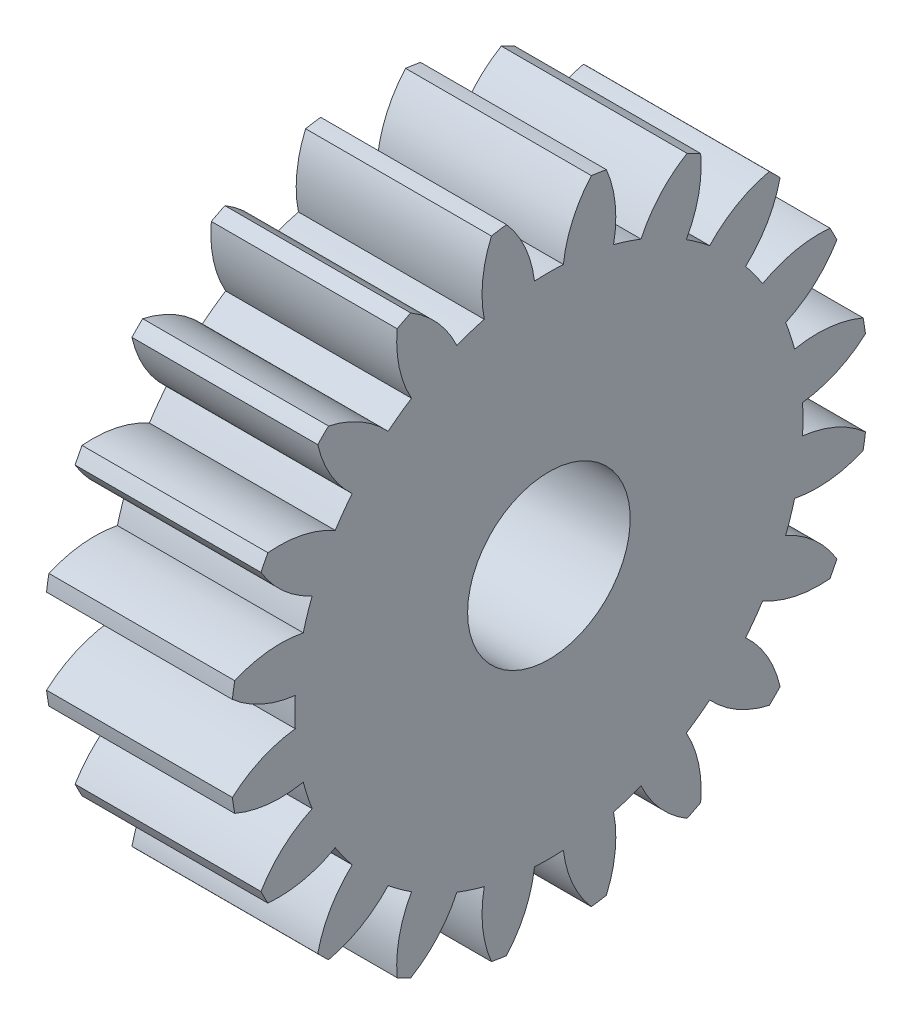
SolidWorks part; units mm, degrees
ref_plane "Plane1" through (0, 0, 0) normal (0, 0, 1) x (1, 0, 0)
ref_plane "Plane2" through (0, 0, 0) normal (0, 1, 0) x (1, 0, 0)
ref_plane "Plane3" through (0, 0, 0) normal (1, 0, 0) x (0, 0, -1)
sketch "HoldingSke" plane through (0, 0, 0) normal (0, 1, 0) x (1, 0, 0)
  line L0 (0, 0) -> (0.7518, -0.2736)
  line L1 (-15, 0) -> (100, 0) construction
  line L2 (0, 0) -> (-2.1039, 2.3779)
  line L3 (0, 0) -> (-11.863, 4.5341)
  line L4 (0, 0) -> (8.1152, 2.9537)
  line L5 (0, 0) -> (-46.8476, -17.4728)
  line L6 (0, 0) -> (-6.6317, -4.4744)
  line L7 (-2.1039, 2.3779) -> (8.6586, 51.2059)
  line L8 (-76.2, 54.61) -> (-75.2, 54.61)
  line L9 (-71.009, 38.7566) -> (-53.1078, 45.2721)
  line L10 (-76.2, 71.12) -> (104.1128, 71.12)
  line L11 (0, 0) -> (-8, 0)
  line L12 (-76.2, 101.6) -> (-76.155, 101.6)
  line L13 (24.9733, 27.94) -> (52.9518, 28.4284)
  line L14 (24.9733, 27.94) -> (24.9743, 27.94)
  line L15 (24.9733, 27.94) -> (100.4006, 29.5858)
  line L16 (-63.627, -1.25) -> (-12.827, -1.25)
  circle A0 centre (0, 0) radius 3.5
  circle A1 centre (0, 0) radius 10.9365
  circle A2 centre (0, 0) radius 37.5
  circle A3 centre (0, 0) radius 3.5
  dimension "MHD" = 21.873
  dimension "Hub_dia" = 75
  dimension "Bore" = 7
  dimension "MBD" = 7
  dimension "Num_teeth" = 20
  dimension "Pitch" = 0.8
  dimension "Overall_len" = 50
  dimension "Show_teeth" = 20
  dimension "Thickness" = 8
  dimension "OAL" = 50.0001
  dimension "T_dim" = 1
  dimension "Ap" = 20
  dimension "H" = 19.05
  dimension "Pitch_radius" = 180.3128
  dimension "Width" = 8
  dimension "Backlash" = 0.045
  dimension "Addendum_fac" = 1
  dimension "Dedendum_fac" = 1.25
  dimension "Clearance_fac" = 0.25
  dimension "Dedendum_add" = 0.001
  dimension "Module" = 1.25
sketch "BasProSke" plane through (0, 0, 0) normal (0, 1, 0) x (1, 0, 0)
  line L0 (-10, 0) -> (60, 0) construction
  line L1 (0, 0) -> (0, 13.75)
  line L2 (0, 0) -> (8, 0)
  line L3 (8, 0) -> (8, 13.75)
  line L4 (8, 13.75) -> (0, 13.75)
  dimension "Thickness" = 8
  dimension "Diameter" = 27.5
revolve "Base-Revolve" add sketch "BasProSke" angle 360 about L0
sketch "TooCutSke" plane through (0, 0, 0) normal (1, 0, 0) x (0, 0, -1)
  line L1 (0, 0) -> (0, 107) construction
  line L2 (0, 0) -> (-1.0594, 12.455) construction
  line L3 (0, 0) -> (-3.9007, 24.6278) construction
  line L4 (-1.0594, 12.455) -> (-1.9503, 12.3139) construction
  arc A0 (0.6211, 10.9188) -> (-0.6211, 10.9188) centre (0, 0) ccw
  arc A1 (1.8466, 13.6511) -> (-1.8466, 13.6511) centre (0, 0) ccw
  circle A2 centre (0, 0) radius 12.5 construction
  circle A3 centre (0, 0) radius 11.7462 construction
  arc A4 (-0.6211, 10.9188) -> (-1.8466, 13.6511) centre (-5.5866, 10.3326) ccw
  arc A5 (1.8466, 13.6511) -> (0.6211, 10.9188) centre (5.5866, 10.3326) ccw
  dimension "Root_dia" = 21.873
  dimension "Overcut_dia" = 27.5508
  dimension "Pitch_dia" = 25
  dimension "Base_dia" = 23.4923
  dimension "Flank_rad" = 5
  dimension "Half_ang" = 9
  dimension "Half_CT" = 0.902
extrude "ToothCut" cut sketch "TooCutSke" along normal through all
fillet "Breaks" [suppressed] radius 0.025
fillet "RootFillets" [suppressed] radius 0.3135
pattern_circular "TeethCuts" count 20 every 18 about axis through (-10, 0, 0) along (1, 0, 0) of "ToothCut", "RootFillets", "Breaks"
sketch "HubNeaOneSke" plane through (0, 0, 0) normal (-1, 0, 0) x (0, 0, 1)
  circle A0 centre (0, 0) radius 10.9365
  dimension "Diameter" = 21.873
extrude "HubNearOne" [suppressed] add sketch "HubNeaOneSke" along normal blind 42.0001
sketch "HubNeaBotSke" plane through (0, 0, 0) normal (-1, 0, 0) x (0, 0, 1)
  circle A0 centre (0, 0) radius 10.9365
  dimension "Diameter" = 21.873
extrude "HubNearBoth" [suppressed] add sketch "HubNeaBotSke" along normal blind 21
ref_plane "FarPln" through (8, 0, 0) normal (1, 0, 0) x (0, 0, -1)
sketch "HubFarSke" plane through (8, 0, 0) normal (1, 0, 0) x (0, 0, -1)
  circle A0 centre (0, 0) radius 10.9365
  dimension "Diameter" = 21.873
extrude "HubFar" [suppressed] add sketch "HubFarSke" along normal blind 21
sketch "BorSke" plane through (0, 0, 0) normal (1, 0, 0) x (0, 0, -1)
  circle A0 centre (0, 0) radius 3.5
  dimension "Diameter" = 7
extrude "Bore" cut sketch "BorSke" along normal mid plane 100.0001
sketch "KeySke" plane through (0, 0, 0) normal (1, 0, 0) x (0, 0, -1)
  line L0 (-1, 0) -> (-1, 4.5)
  line L1 (-1, 4.5) -> (1, 4.5)
  line L2 (1, 4.5) -> (1, 0)
  line L3 (0, 0) -> (0, 34) construction
  line L4 (-1, 0) -> (1, 0)
  dimension "Offset" = 4.5
  dimension "Width" = 2
extrude "Keyway" [suppressed] cut sketch "KeySke" along normal mid plane 100.0001
pattern_circular "Keyway2" [suppressed] count 2 every 90 about axis through (-10, 0, 0) along (1, 0, 0)
equation "' \"Module@HoldingSke\" = 6.35"
equation "' \"Num_teeth@HoldingSke\" = 12"
equation "' \"Ap@HoldingSke\" =  20"
equation "' \"Ap@HoldingSke\" = 20"
equation "' \"Width@HoldingSke\" = 0.5 * 25.4"
equation "' \"Hub_dia@HoldingSke\"= 1 * 25.4"
equation "' \"Hub_dia@HoldingSke\" = 1 * 25.4"
equation "' \"Overall_len@HoldingSke\" = 1.0 * 25.4"
equation "' \"Bore@HoldingSke\" = 0.75 * 25.4"
equation "' \"T_dim@HoldingSke\" = 0.1 * 25.4"
equation "' \"Width@KeySke\" = 0.25 * 25.4"
equation "' \"Show_teeth@HoldingSke\" = 13"
equation "' \"Backlash@HoldingSke\" = 0.009 * 25.4"
equation "' \"Addendum_fac@HoldingSke\" = 1.0"
equation "' \"Dedendum_fac@HoldingSke\" = 1.25"
equation "' \"Dedendum_add@HoldingSke\" = 0.00005 * 25.4"
equation "' \"Clearance_fac@HoldingSke\" = 0.25"
equation "\"Pitch@HoldingSke\" = 1 / \"Module@HoldingSke\""
equation "\"Overcut_dia@TooCutSke\" = (\"Num_teeth@HoldingSke\" + 2 * \"Addendum_fac@HoldingSke\") / \"Pitch@HoldingSke\" + 0.002 * 25.4"
equation "\"Pitch_dia@TooCutSke\" = \"Num_teeth@HoldingSke\" / \"Pitch@HoldingSke\""
equation "\"Base_dia@TooCutSke\" = \"Num_teeth@HoldingSke\" / \"Pitch@HoldingSke\" * cos((\"Ap@HoldingSke\"  * 3.14159265 / 180))"
equation "\"Root_dia@TooCutSke\" = (\"Num_teeth@HoldingSke\" + 2) / \"Pitch@HoldingSke\" - 2 * (\"Addendum_fac@HoldingSke\" + \"Dedendum_fac@HoldingSke\") / \"Pitch@HoldingSke\" - \"Dedendum_add@HoldingSke\" * 2"
equation "\"Half_ang@TooCutSke\" = 180 / \"Num_teeth@HoldingSke\""
equation "\"Half_CT@TooCutSke\" = \"Num_teeth@HoldingSke\" / \"Pitch@HoldingSke\" * sin((3.14159265 / 2 / \"Num_teeth@HoldingSke\")) / 2 - 7 * \"Backlash@HoldingSke\" / 4"
equation "\"Flank_rad@TooCutSke\" = \"Num_teeth@HoldingSke\" / \"Pitch@HoldingSke\" / 5"
equation "\"Radius@RootFillets\" = \"Clearance_fac@HoldingSke\" / \"Pitch@HoldingSke\" + \"Dedendum_add@HoldingSke\""
equation "\"Break_rad@Breaks\" = 0.02 / \"Pitch@HoldingSke\""
equation "\"Thickness@HoldingSke\" = \"Width@HoldingSke\""
equation "\"OAL@HoldingSke\" = \"Thickness@HoldingSke\""
equation "\"MHD@HoldingSke\" = (\"Num_teeth@HoldingSke\" + 2) / \"Pitch@HoldingSke\" - 2 * (\"Addendum_fac@HoldingSke\" + \"Dedendum_fac@HoldingSke\")  / \"Pitch@HoldingSke\" - \"Dedendum_add@HoldingSke\" * 2"
equation "\"MBD@HoldingSke\" = (\"Num_teeth@HoldingSke\" + 2) / \"Pitch@HoldingSke\" - 2 * (\"Addendum_fac@HoldingSke\" + \"Dedendum_fac@HoldingSke\")  / \"Pitch@HoldingSke\" - \"Dedendum_add@HoldingSke\" * 2 - 0.002 * 25.4"
equation "\"MHD@HoldingSke\" = ((sgn( \"MHD@HoldingSke\" - \"Hub_dia@HoldingSke\" )-1)*( \"MHD@HoldingSke\" - \"Hub_dia@HoldingSke\" ))/-2+ \"Hub_dia@HoldingSke\""
equation "\"MBD@HoldingSke\" = ((sgn( \"MBD@HoldingSke\" - \"Bore@HoldingSke\" )-1)*( \"MBD@HoldingSke\" - \"Bore@HoldingSke\" ))/-2+ \"Bore@HoldingSke\""
equation "\"OAL@HoldingSke\" = ((sgn( \"OAL@HoldingSke\" - \"Overall_len@HoldingSke\" )+1)*( \"OAL@HoldingSke\" - \"Overall_len@HoldingSke\" ))/2 + \"Overall_len@HoldingSke\" + 0.000002 * 25.4"
equation "\"Num_teeth@TeethCuts\" = int( \"Show_teeth@HoldingSke\" ) + 1"
equation "\"Num_teeth@TeethCuts\" = ((sgn( \"Num_teeth@TeethCuts\" - \"Num_teeth@HoldingSke\" )-1)*( \"Num_teeth@TeethCuts\" - \"Num_teeth@HoldingSke\" ))/-2+ \"Num_teeth@HoldingSke\""
equation "\"Num_teeth@TeethCuts\" = ((sgn( \"Num_teeth@TeethCuts\" - 2.0)+1)*( \"Num_teeth@TeethCuts\" - 2.0))/2 +2.0"
equation "\"Angle@TeethCuts\" = 360.0 / \"Num_teeth@HoldingSke\""
equation "\"Diameter@BasProSke\" = (\"Num_teeth@HoldingSke\" + 2 * \"Addendum_fac@HoldingSke\") / \"Pitch@HoldingSke\""
equation "\"Thickness@BasProSke\"  = \"Thickness@HoldingSke\""
equation "' \"Fillet_rad@BasProSke\" =  \"Thickness@HoldingSke\" * 0.05"
equation "' \"Fillet_rad@BasProSke\" = \"Thickness@HoldingSke\" * 0.05"
equation "\"MHD@HoldingSke\" = ((sgn( \"MHD@HoldingSke\" - \"Root_dia@TooCutSke\" )-1)*( \"MHD@HoldingSke\" - \"Root_dia@TooCutSke\" ))/-2+ \"Root_dia@TooCutSke\""
equation "\"Diameter@HubNeaOneSke\" = \"MHD@HoldingSke\""
equation "\"Length@HubNearOne\" = \"OAL@HoldingSke\" - \"Thickness@BasProSke\""
equation "\"Diameter@HubNeaBotSke\" = \"MHD@HoldingSke\""
equation "\"Length@HubNearBoth\" = ( \"OAL@HoldingSke\" - \"Thickness@BasProSke\" ) / 2.0"
equation "\"Thickness@FarPln\" = \"Thickness@BasProSke\""
equation "\"Diameter@HubFarSke\" = \"MHD@HoldingSke\""
equation "\"Length@HubFar\" = ( \"OAL@HoldingSke\" - \"Thickness@BasProSke\" ) / 2.0"
equation "\"Diameter@BorSke\" = \"MBD@HoldingSke\""
equation "\"D1@Bore\" = \"OAL@HoldingSke\" * 2.0"
equation "\"D1@Keyway\" = \"OAL@HoldingSke\" * 2.0"
equation "\"Offset@KeySke\" = \"T_dim@HoldingSke\" + \"MBD@HoldingSke\" / 2.0"
